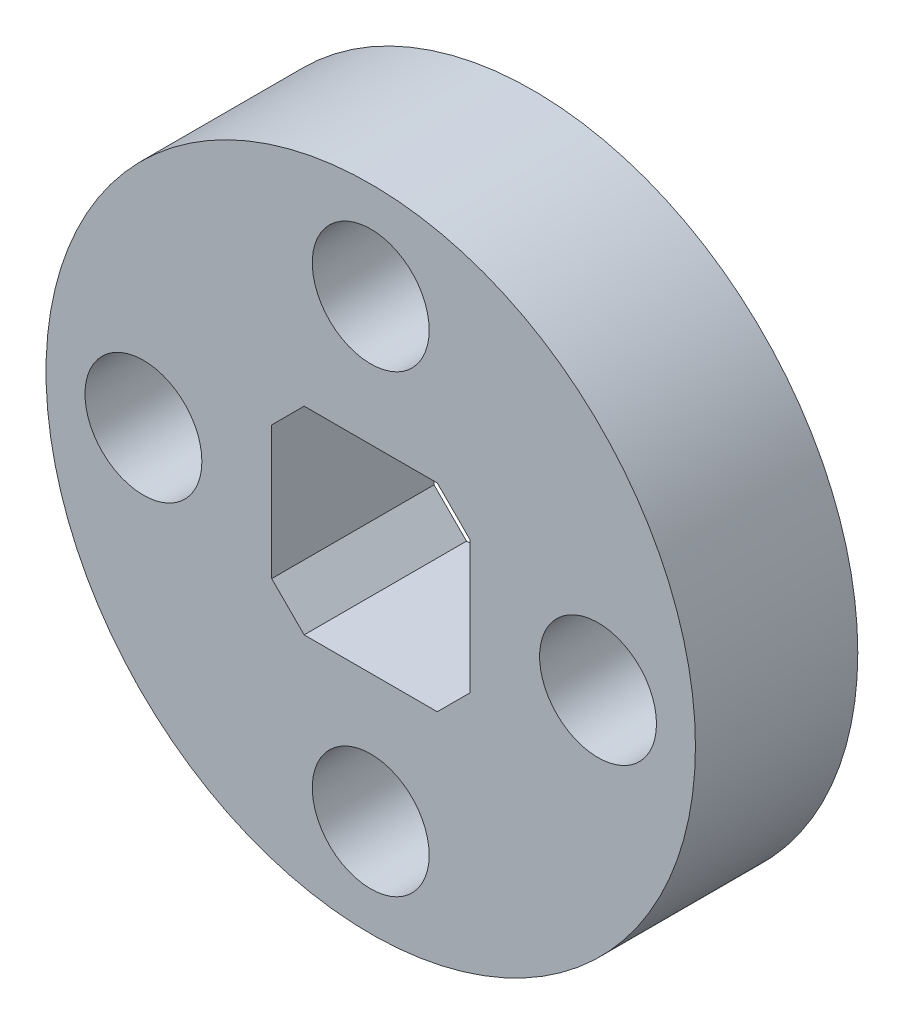
SolidWorks part; units mm, degrees
ref_plane "Plan de face" through (0, 0, 0) normal (0, 0, 1) x (1, 0, 0)
ref_plane "Plan de dessus" through (0, 0, 0) normal (0, 1, 0) x (1, 0, 0)
ref_plane "Plan de droite" through (0, 0, 0) normal (1, 0, 0) x (0, 0, -1)
sketch "Esquisse1" plane through (0, 0, 0) normal (0, 0, 1) x (1, 0, 0)
  line L0 (-3.05, 0) -> (3.05, 0) construction
  line L1 (0, -3.05) -> (0, 3.05) construction
  line L2 (-3.05, 3.05) -> (3.05, 3.05)
  line L3 (3.05, 3.05) -> (3.05, -3.05)
  line L4 (-3.05, 3.05) -> (-3.05, -3.05)
  line L5 (-3.05, -3.05) -> (3.05, -3.05)
  circle A0 centre (0, 0) radius 10
  dimension "D1" = 20
  dimension "D2" = 6.1
  dimension "D3" = 6.1
extrude "Boss.-Extru.1" add sketch "Esquisse1" along normal blind 5
sketch "Esquisse2" plane through (0, 0, 5) normal (0, 0, 1) x (1, 0, 0)
  line L0 (0, 0) -> (0, 7) construction
  circle A0 centre (0, 7) radius 1.8
  circle A1 centre (7, 0) radius 1.8
  circle A2 centre (0, -7) radius 1.8
  circle A3 centre (-7, 0) radius 1.8
  point P4 (-8.0311, 0)
  point P5 (0, 0)
  point P13 (0, 0)
  dimension "D1" = 3.6
  dimension "D2" = 7
  dimension "D3" = 4
extrude "Enlèv. mat.-Extru.1" cut sketch "Esquisse2" against normal through all both and the other way through all
chamfer "Chanfrein1" distance 1 angle 45 4 edges at (-3.05, 3.05, 2.5) (3.05, 3.05, 2.5) (3.05, -3.05, 2.5) (-3.05, -3.05, 2.5)
